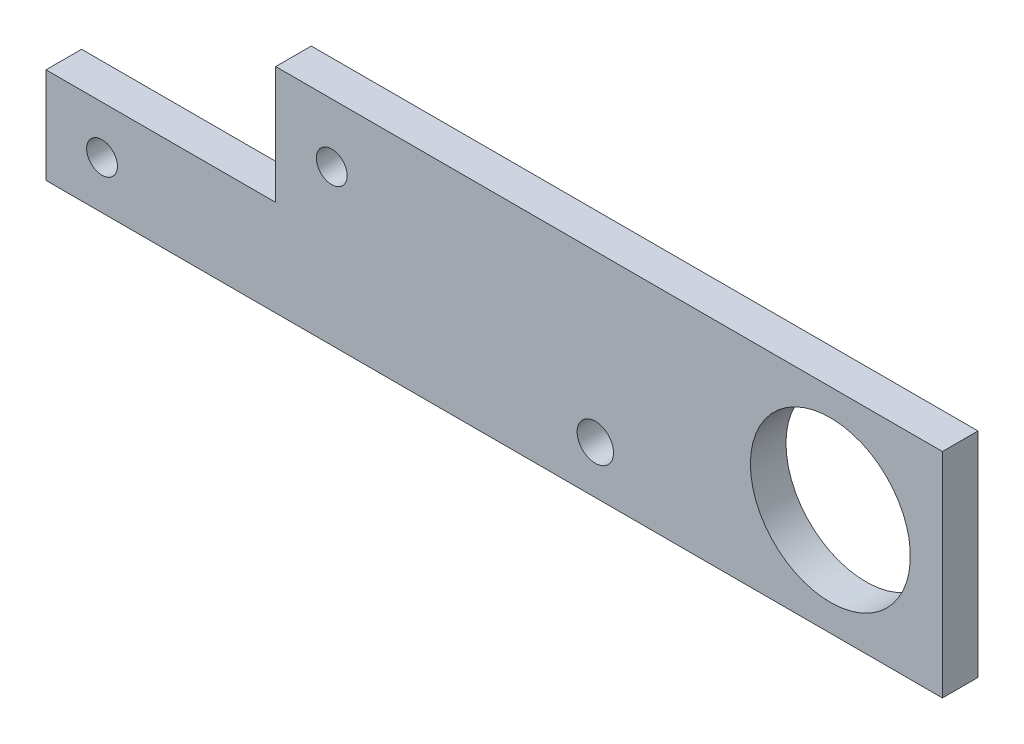
SolidWorks part; units mm, degrees
ref_plane "Front Plane" through (0, 0, 0) normal (0, 0, 1) x (1, 0, 0)
ref_plane "Top Plane" through (0, 0, 0) normal (0, 1, 0) x (1, 0, 0)
ref_plane "Right Plane" through (0, 0, 0) normal (1, 0, 0) x (0, 0, -1)
sketch "Sketch1" plane through (0, 0, 0) normal (0, 0, 1) x (1, 0, 0)
  line L1 (0, 0) -> (160, 0)
  line L2 (0, 0) -> (0, -38.1)
  line L3 (0, -38.1) -> (160, -38.1)
  line L4 (160, 0) -> (160, -38.1)
  dimension "D1" = 38.1
  dimension "D2" = 160
extrude "Boss-Extrude1" add sketch "Sketch1" along normal blind 6.35
sketch "Sketch2" plane through (0, 0, 0) normal (0, 0, -1) x (-1, 0, 0)
  line L0 (-160, -38.1) -> (-160, 0) construction
  circle A0 centre (-140, -19.05) radius 14.275
  point P5 (-160, -19.05)
  dimension "D1" = 28.55
  dimension "D2" = 20
extrude "Cut-Extrude1" cut sketch "Sketch2" against normal through all
sketch "Sketch3" plane through (0, 0, 6.35) normal (0, 0, 1) x (1, 0, 0)
  line L1 (0, 0) -> (41, 0)
  line L2 (0, 0) -> (0, -21)
  line L3 (0, -21) -> (41, -21)
  line L4 (41, 0) -> (41, -21)
  dimension "D1" = 21
  dimension "D2" = 41
extrude "Cut-Extrude2" cut sketch "Sketch3" against normal through all
sketch "Sketch4" plane through (0, 0, 6.35) normal (0, 0, 1) x (1, 0, 0)
  line L0 (0, -21) -> (0, -38.1) construction
  line L1 (41, -21) -> (41, 0) construction
  circle A0 centre (10, -29.55) radius 2.75
  circle A1 centre (51, -10.5) radius 2.75
  circle A2 centre (98.0496, -29.55) radius 3.25
  point P4 (0, -29.55)
  point P9 (41, -10.5)
  point P12 (98.0496, -29.55)
  dimension "D2" = 5.5
  dimension "D3" = 5.5
  dimension "D5" = 6.5
  dimension "D1" = 10
  dimension "D4" = 10
extrude "Cut-Extrude3" cut sketch "Sketch4" against normal through all
